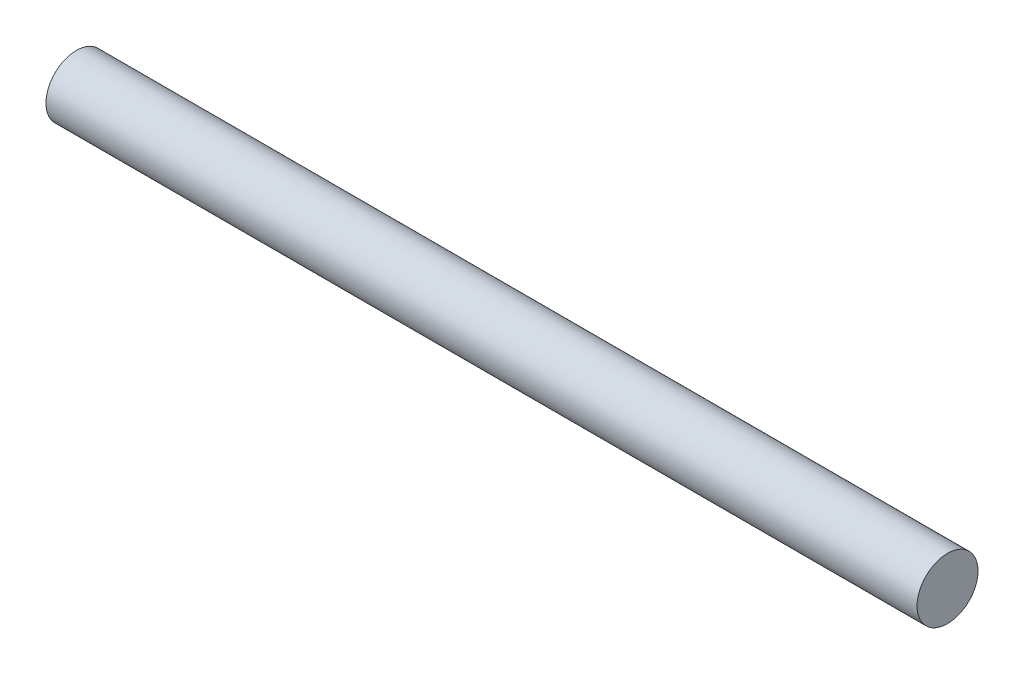
SolidWorks part; units mm, degrees
ref_plane "Front Plane" through (0, 0, 0) normal (0, 0, 1) x (1, 0, 0)
ref_plane "Top Plane" through (0, 0, 0) normal (0, 1, 0) x (1, 0, 0)
ref_plane "Right Plane" through (0, 0, 0) normal (1, 0, 0) x (0, 0, -1)
sketch "Sketch1" plane through (0, 0, 0) normal (1, 0, 0) x (0, 0, -1)
  circle A0 centre (0, 0) radius 17.5
  dimension "D1" = 35
extrude "Boss-Extrude1" add sketch "Sketch1" along normal mid plane 500
